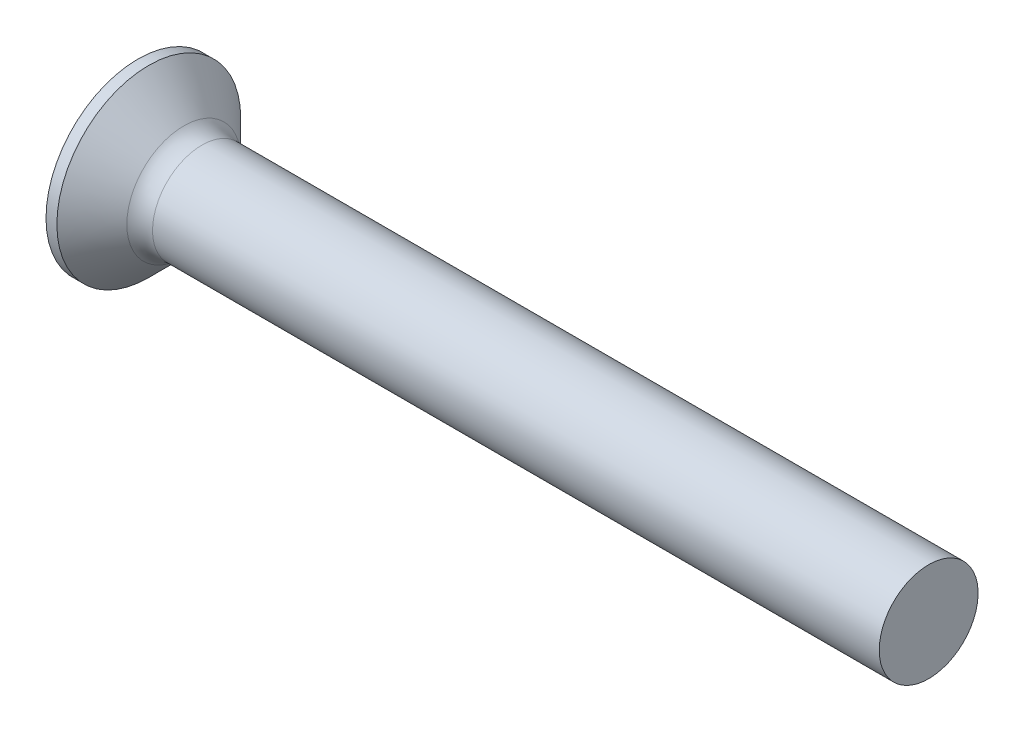
SolidWorks part; units mm, degrees
ref_plane "Plane1" through (0, 0, 0) normal (0, 0, 1) x (1, 0, 0)
ref_plane "Plane2" through (0, 0, 0) normal (0, 1, 0) x (1, 0, 0)
ref_plane "Plane3" through (0, 0, 0) normal (1, 0, 0) x (0, 0, -1)
revolve "Base-Revolve" add sketch "BodySke"
sketch "BodySke" plane through (0, 0, 0) normal (0, 0, 1) x (1, 0, 0)
  line L0 (0, 0) -> (0, 4.65)
  line L1 (0, 4.65) -> (0.55, 4.65)
  line L2 (2.7, 2.5) -> (40, 2.5)
  line L3 (40, 2.5) -> (40, 0)
  line L4 (40, 0) -> (0, 0)
  line L5 (-6.35, 0) -> (82.55, 0) construction
  line L6 (2.7, -2.5) -> (40, -2.5) construction
  line L7 (0.55, -4.65) -> (2.7, -2.5) construction
  line L8 (0.55, 4.65) -> (2.7, 2.5)
  line L9 (0, -4.65) -> (0.55, -4.65) construction
  line L10 (3.5, 4.0875) -> (3.5, -5.4375) construction
  line L11 (0, 6.35) -> (0, -3.175) construction
  dimension "Diameter" = 5
  dimension "Length" = 40
  dimension "Head_ht" = 2.7
  dimension "Head_dia" = 9.3
  dimension "Head_ang" = 90
  dimension "D6" = 0.55
  dimension "Advance" = 0.8
  dimension "Thread_nom" = 40
cosmetic thread "ThreadCosmetic"
fillet "Fillet1" radius 1.3 1 edges at (2.7, 0, 2.5)
sketch "Sketch3" plane through (0, 0, 0) normal (-1, 0, 0) x (0, 0, 1)
  line L0 (-0.515, 2.45) -> (0.515, 2.45)
  line L1 (0.515, 2.45) -> (0.515, -2.45)
  line L2 (0.515, -2.45) -> (-0.515, -2.45)
  line L3 (-0.515, -2.45) -> (-0.515, 2.45)
  dimension "D1" = 2.45
  dimension "Cross_dia" = 4.9
  dimension "D2" = 0.515
  dimension "Cross_width" = 1.03
ref_plane "Plane4" through (3.05, 0, 0) normal (-1, 0, 0) x (0, 0, 1)
sketch "Sketch4" plane through (3.05, 0, 0) normal (-1, 0, 0) x (0, 0, 1)
  line L0 (-0.515, 0.9293) -> (0.515, 0.9293)
  line L3 (0.515, 0.9293) -> (0.515, -0.9293)
  line L4 (0.515, -0.9293) -> (-0.515, -0.9293)
  line L5 (-0.515, -0.9293) -> (-0.515, 0.9293)
  dimension "D1" = 1.03
  dimension "D2" = 1.8587
  dimension "D3" = 0.515
  dimension "D4" = 0.9293
loft "Recess" cut profiles "Sketch3", "Sketch4"
pattern_circular "RecPat" count 2 every 90 about axis through (0, 0, 0) along (1, 0, 0) of "Recess"
sketch "RecCorSke" plane through (0, 0, 0) normal (0, 0, 1) x (1, 0, 0)
  line L0 (-3.175, 0) -> (15.875, 0) construction
  line L2 (0, 0) -> (0, 1.0643)
  line L3 (0, 1.0643) -> (3.05, 0.851)
  line L4 (3.05, 0.851) -> (3.3265, 0)
  line L5 (3.3265, 0) -> (0, 0)
  dimension "Diameter" = 1.702
  dimension "Depth" = 3.05
  dimension "Draft_angle" = 4
  dimension "Bottom_angle" = 18
revolve "RecessCore" cut sketch "RecCorSke" angle 360 about L0
sketch "ThdSchSke" plane through (0, 0, 0) normal (0, 0, 1) x (1, 0, 0)
  line L0 (3.5, -2.055) -> (3.1884, -2.5)
  line L1 (3.5, -2.055) -> (3.8116, -2.5)
  line L2 (3.8116, -2.5) -> (3.8116, -3.125)
  line L3 (-3.175, 0) -> (5.1513, 0) construction
  line L5 (3.8116, -3.125) -> (3.1884, -3.125)
  line L6 (3.1884, -3.125) -> (3.1884, -2.5)
  line L7 (0, 4.65) -> (0, -4.65) construction
  dimension "Thread_minor" = 4.11
  dimension "Diameter" = 5
  dimension "Start" = 3.5
  dimension "SideAngle" = 55
  dimension "VeeAngle" = 70
  dimension "Overcut" = 6.25
revolve "ThreadSchematic" [suppressed] cut sketch "ThdSchSke" angle 360 about L3
pattern_linear "ThdSchPat" [suppressed]
equation "\"D1@Sketch3\" = \"Cross_dia@Sketch3\" / 2"
equation "\"D2@Sketch3\" = \"Cross_width@Sketch3\" / 2"
equation "\"Depth@RecCorSke\" = \"Cross_depth@Plane4\""
equation "\"D1@Sketch4\" = \"Cross_width@Sketch3\""
equation "\"D2@Sketch4\" = \"Cross_dia@Sketch3\" - 2.0 * \"Cross_depth@Plane4\" * tan(26.5  * 0.017453292)"
equation "\"D3@Sketch4\" = \"D1@Sketch4\" / 2"
equation "\"D4@Sketch4\" = \"D2@Sketch4\" / 2"
equation "\"Thread_length@ThreadCosmetic\" = ((sgn( (\"Length@BodySke\" - \"Advance@BodySke\" * 1.0 - \"Head_ht@BodySke\" ) - \"Thread_nom@BodySke\" )-1)*( (\"Length@BodySke\" - \"Advance@BodySke\" * 1.0 - \"Head_ht@BodySke\" ) - \"Thread_nom@BodySke\" ))/-2+ \"Thread_nom@BodySke\""
equation "\"Thread_minor@ThdSchSke\" = \"Thread_minor@ThreadCosmetic\""
equation "\"Diameter@ThdSchSke\" = \"Diameter@BodySke\""
equation "\"Overcut@ThdSchSke\" = \"Diameter@BodySke\" * 1.25"
equation "\"Start@ThdSchSke\" = 0.000001 + \"Length@BodySke\" - \"Thread_length@ThreadCosmetic\"  '---Countersunk---"
equation "\"Num_threads@ThdSchPat\" = int( \"Thread_length@ThreadCosmetic\" / \"Advance@BodySke\" + 0.999 )  + 1"
equation "\"Advance@ThdSchPat\" = \"Thread_length@ThreadCosmetic\" /  (\"Num_threads@ThdSchPat\" - 1) 'relax it"
